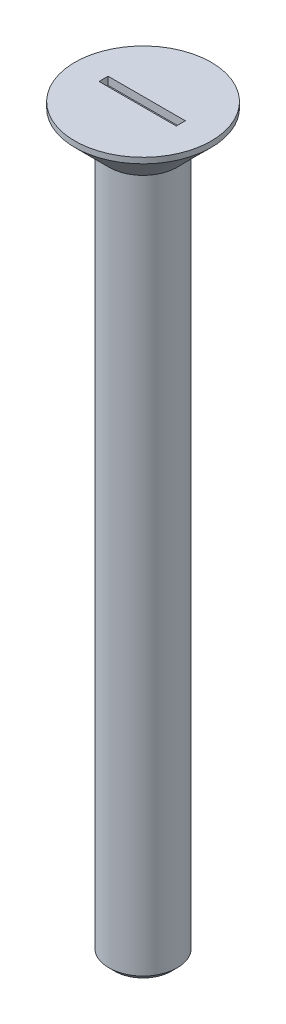
SolidWorks part; units mm, degrees
ref_plane "前基準面" through (0, 0, 0) normal (0, 0, 1) x (1, 0, 0)
ref_plane "上基準面" through (0, 0, 0) normal (0, 1, 0) x (1, 0, 0)
ref_plane "右基準面" through (0, 0, 0) normal (1, 0, 0) x (0, 0, -1)
sketch "草圖1" plane through (0, 0, 0) normal (0, 0, 1) x (1, 0, 0)
  line L0 (0, -8.5328) -> (0, 41.0766) construction
  line L3 (0, 65) -> (6, 65)
  line L4 (6, 65) -> (6, 64.5)
  line L5 (3, 61.5) -> (3, 0)
  line L6 (0, 0) -> (3, 0)
  line L7 (0, 0) -> (0, 65)
  line L8 (6, 64.5) -> (3, 61.5)
  dimension "D1" = 65
  dimension "D2" = 0.5
  dimension "D3" = 3
  dimension "D4" = 6
  dimension "D5" = 45
revolve "旋轉1" add sketch "草圖1" angle 360 about L0
sketch "草圖2" plane through (0, 65, 0) normal (0, 1, 0) x (-1, 0, 0)
  line L1 (3.4719, 0.4) -> (-3.3206, 0.4)
  line L2 (3.4719, 0.4) -> (3.4719, -0.4)
  line L3 (3.4719, -0.4) -> (-3.3206, -0.4)
  line L4 (-3.3206, 0.4) -> (-3.3206, -0.4)
  circle A0 centre (0, 0) radius 6 construction
  dimension "D1" = 0.8
  dimension "D2" = 0.4
extrude "除料-伸長1" cut sketch "草圖2" against normal blind 0.7
chamfer "導角1" distance 0.5 angle 45 1 edges at (0, 0, -3)
